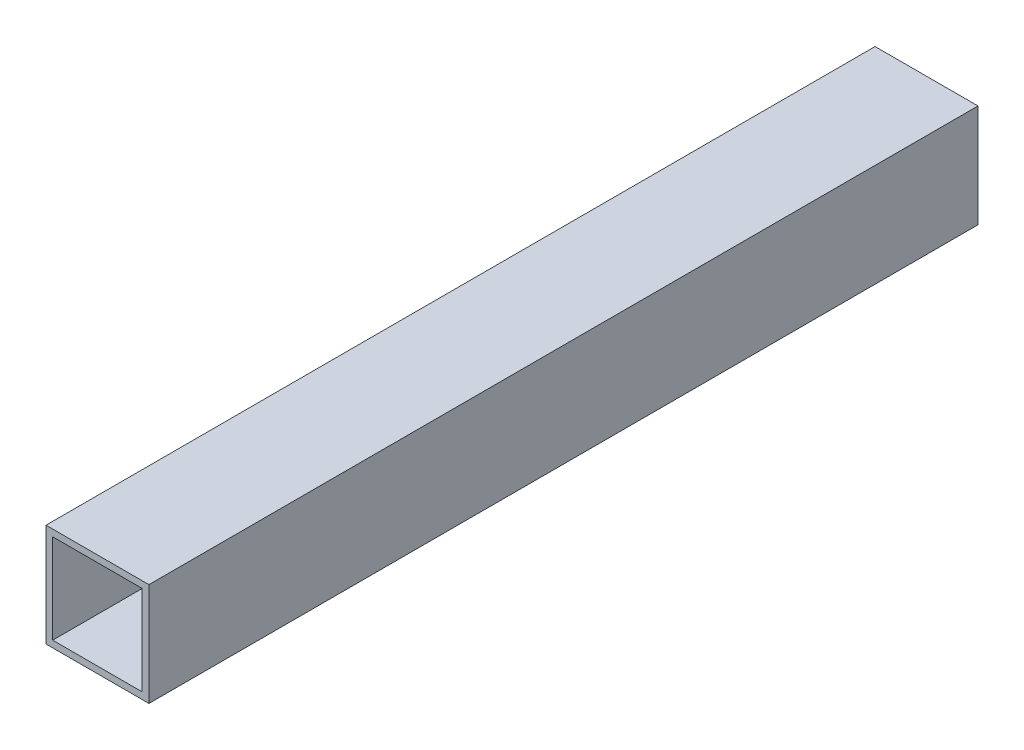
SolidWorks part; units mm, degrees
ref_plane "Front Plane" through (0, 0, 0) normal (0, 0, 1) x (1, 0, 0)
ref_plane "Top Plane" through (0, 0, 0) normal (0, 1, 0) x (1, 0, 0)
ref_plane "Right Plane" through (0, 0, 0) normal (1, 0, 0) x (0, 0, -1)
sketch "Sketch1" plane through (0, 0, 0) normal (0, 0, 1) x (1, 0, 0)
  line L1 (11.049, 11.049) -> (-11.049, 11.049)
  line L2 (11.049, 11.049) -> (11.049, -11.049)
  line L3 (11.049, -11.049) -> (-11.049, -11.049)
  line L4 (-11.049, 11.049) -> (-11.049, -11.049)
  line L5 (11.049, 11.049) -> (-11.049, -11.049) construction
  line L6 (11.049, -11.049) -> (-11.049, 11.049) construction
  line L7 (12.7, 12.7) -> (-12.7, 12.7)
  line L8 (12.7, 12.7) -> (12.7, -12.7)
  line L9 (12.7, -12.7) -> (-12.7, -12.7)
  line L10 (-12.7, 12.7) -> (-12.7, -12.7)
  line L11 (12.7, 12.7) -> (-12.7, -12.7) construction
  line L12 (12.7, -12.7) -> (-12.7, 12.7) construction
  point P0 (0, 0)
  point P6 (0, 0)
  dimension "D3" = 1.651
  dimension "D4" = 1.651
  dimension "D5" = 1.651
  dimension "D2" = 25.4
  dimension "D1" = 25.4
extrude "Boss-Extrude1" add sketch "Sketch1" along normal up to vertex (204.6 mm away)
sketch "Sketch3" plane through (0, 0, 0) normal (0, 1, 0) x (1, 0, 0)
  line L0 (0, 12.8662) -> (0, -262.1311) construction
  line L1 (0, -13.97) -> (0, 13.97) construction
ref_point "Point1"
equation "\"c1c2Len\"= 250"
equation "\"D1\"= \"c1c2Len\""
equation "\"1inchSquareTubeLen\"=25.4"
equation "\"D2@Sketch1\"=\"1inchSquareTubeLen\""
equation "\"D1@Sketch1\"=\"1inchSquareTubeLen\""
equation "\"squareTubeWallThickness\"=1.651"
equation "\"D5@Sketch1\"=\"squareTubeWallThickness\""
equation "\"D4@Sketch1\"=\"squareTubeWallThickness\""
equation "\"D3@Sketch1\"=\"squareTubeWallThickness\""
